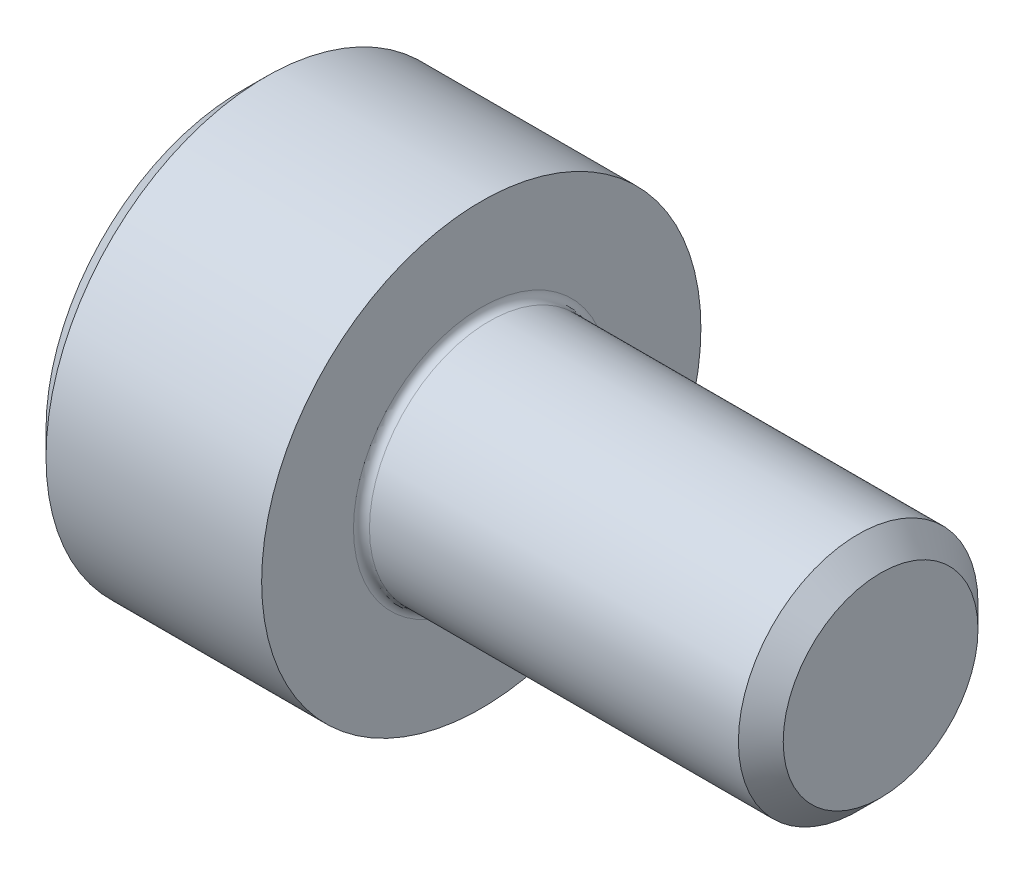
SolidWorks part; units mm, degrees
revolve "Base-Revolve" add sketch "BodySke"
sketch "BodySke" plane through (0, 0, 0) normal (0, 0, 1) x (1, 0, 0)
  line L0 (0, 0) -> (0, 2.45)
  line L1 (0.3, 2.75) -> (3, 2.75)
  line L2 (3, 2.75) -> (3, 1.5)
  line L3 (3, 1.5) -> (7.7195, 1.5)
  line L4 (8, 1.2195) -> (8, 0)
  line L5 (8, 0) -> (0, 0)
  line L6 (-31.75, 0) -> (127, 0) construction
  line L7 (0, 2.45) -> (0.3, 2.75)
  line L8 (8, 1.2195) -> (7.7195, 1.5)
  line L9 (0, -2.45) -> (0.3, -2.75) construction
  line L10 (8, -1.2195) -> (7.7195, -1.5) construction
  line L11 (3.5, 9.525) -> (3.5, 3.175) construction
  line L12 (3, 9.525) -> (3, 3.175) construction
  line L13 (-42, 9.525) -> (-42, 3.175) construction
  dimension "Diameter" = 3
  dimension "Head_ht" = 3
  dimension "Length" = 5
  dimension "Body_ch_ang" = 45
  dimension "Head_dia" = 5.5
  dimension "Head_ch_ang" = 45
  dimension "Minor_dia" = 2.439
  dimension "Advance" = 0.5
  dimension "Thread_nom" = 5
  dimension "Thread_length" = 50
  dimension "Head_ch_ht" = 0.3
cosmetic thread "ThreadCosmetic" [suppressed]
fillet "Fillet1" radius 0.1 1 edges at (3, 0, 1.5)
material "AISI 1035 鋼 (SS)"
ref_plane "Plane1" through (0, 0, 0) normal (0, 0, 1) x (1, 0, 0)
ref_plane "Plane2" through (0, 0, 0) normal (0, 1, 0) x (1, 0, 0)
ref_plane "Plane3" through (0, 0, 0) normal (1, 0, 0) x (0, 0, -1)
sketch "Sketch2" plane through (0, 0, 0) normal (0, 0, 1) x (1, 0, 0)
  line L0 (0, 1.28) -> (1.3, 1.28)
  line L1 (1.3, 1.28) -> (2.039, 0)
  line L2 (-31.75, 0) -> (127, 0) construction
  line L3 (2.039, 0) -> (0, 0)
  line L4 (0, 0) -> (0, 1.28)
  line L5 (0, 2.45) -> (0, -2.45) construction
  line L6 (0, 0) -> (47.625, 0) construction
  line L7 (3, -2.75) -> (3, 2.75) construction
  dimension "D1" = 1.28
  dimension "D2" = 60
revolve "Hex-PreBroach" cut sketch "Sketch2" angle 360 about L6
sketch "Sketch3" plane through (0, 0, 0) normal (-1, 0, 0) x (0, 0.5, 0.866)
  line L0 (0.739, 1.28) -> (-0.739, 1.28)
  line L1 (-0.739, 1.28) -> (-1.478, 0)
  line L2 (0.739, 1.28) -> (1.478, 0)
  line L3 (0.739, -1.28) -> (1.478, 0)
  line L4 (0.739, -1.28) -> (-0.739, -1.28)
  line L5 (-0.739, -1.28) -> (-1.478, 0)
  dimension "D1" = 1.28
  dimension "D2" = 1.28
  dimension "Hex_size" = 2.56
extrude "Hex" cut sketch "Sketch3" against normal blind 1.3
sketch "Sketch4" plane through (0, 0, 0) normal (-1, 0, 0) x (0, 0, 1)
  line L0 (0, 0) -> (1.4605, 0)
  line L1 (0, 0) -> (6.1484, 3.5498) construction
  line L2 (0, 0) -> (0.7302, 1.2648)
  line L3 (1.2009, 0.3267) -> (1.3933, 0.4378)
  line L4 (0.8834, 0.8767) -> (1.0758, 0.9877)
  arc A0 (1.2009, 0.3267) -> (0.8834, 0.8767) centre (0, 0) ccw
  arc A1 (1.4605, 0) -> (1.3933, 0.4378) centre (0, 0) ccw
  arc A2 (0.7302, 1.2648) -> (1.0758, 0.9877) centre (0, 0) cw
  dimension "D1" = 30
  dimension "D2" = 60
  dimension "Spline_p_dim" = 0.635
  dimension "D3" = 0.3175
extrude "Spline" [suppressed] cut sketch "Sketch4" against normal blind 1.3
pattern_circular "CirPattern1" [suppressed] count 6 every 60
sketch "Sketch5" plane through (0, 0, 0) normal (0, 0, 1) x (1, 0, 0)
  line L0 (-31.75, 0) -> (127, 0) construction
  line L2 (0, 2.45) -> (0, -2.45) construction
  circle A0 centre (1.2, 0) radius 0.475
  dimension "Drilled_hole_dia" = 0.95
  dimension "Drilled_hole_loc" = 1.2
extrude "Hole" [suppressed] cut sketch "Sketch5" against normal through all and the other way through all
pattern_circular "Drilled-4" [suppressed] count 2 every 60
pattern_circular "Drilled-6" [suppressed] count 3 every 60
sketch "ThdSchSke" plane through (0, 0, 0) normal (0, 0, 1) x (1, 0, 0)
  line L0 (3.5, -1.2195) -> (3.3036, -1.5)
  line L1 (3.5, -1.2195) -> (3.6964, -1.5)
  line L2 (3.6964, -1.5) -> (3.6964, -1.875)
  line L3 (-3.175, 0) -> (5.1513, 0) construction
  line L5 (3.6964, -1.875) -> (3.3036, -1.875)
  line L6 (3.3036, -1.875) -> (3.3036, -1.5)
  line L7 (0, 2.45) -> (0, -2.45) construction
  dimension "Thread_minor" = 2.439
  dimension "Diameter" = 3
  dimension "Start" = 3.5
revolve "ThreadSchematic" [suppressed] cut sketch "ThdSchSke" angle 360 about L3
pattern_linear "ThdSchPat" [suppressed]
equation "\"D2@Sketch3\" = \"Hex_size@Sketch3\" / 2"
equation "\"D1@Sketch3\" = \"Hex_size@Sketch3\" / 2"
equation "\"D1@Sketch2\" = \"Hex_size@Sketch3\" / 2"
equation "\"D3@Sketch4\" = \"Spline_p_dim@Sketch4\" / 2"
equation "\"Thread_minor@ThreadCosmetic\"  =  \"Minor_dia@BodySke\""
equation "\"D2@CirPattern1\" = 360 / \"Num_teeth@CirPattern1\""
equation "\"Wall_thickness@Sketch2\" = \"Head_ht@BodySke\" - \"Key_eng@Hex\""
equation "\"Thread_length@ThreadCosmetic\" = ((sgn( (\"Length@BodySke\" - \"Advance@BodySke\" ) - \"Thread_nom@BodySke\" )-1)*( (\"Length@BodySke\" - \"Advance@BodySke\" ) - \"Thread_nom@BodySke\" ))/-2+ \"Thread_nom@BodySke\""
equation "\"Thread_minor@ThdSchSke\" = \"Minor_dia@BodySke\""
equation "\"Diameter@ThdSchSke\" = \"Diameter@BodySke\""
equation "\"Overcut@ThdSchSke\" = \"Diameter@BodySke\" * 1.25"
equation "\"Start@ThdSchSke\" = \"Head_ht@BodySke\" + \"Length@BodySke\" - \"Thread_length@ThreadCosmetic\"  '---Non-countersunk---"
equation "\"Num_threads@ThdSchPat\" = int( \"Thread_length@ThreadCosmetic\" / \"Advance@BodySke\" + 0.999 )  + 1"
equation "\"Advance@ThdSchPat\" = \"Thread_length@ThreadCosmetic\" /  (\"Num_threads@ThdSchPat\" - 1) 'relax it"
equation "\"Num_threads@ThdSchPat\" = \"Num_threads@ThdSchPat\" - sgn( \"Num_threads@ThdSchPat\" - 1) '---chamfered tips only---"
